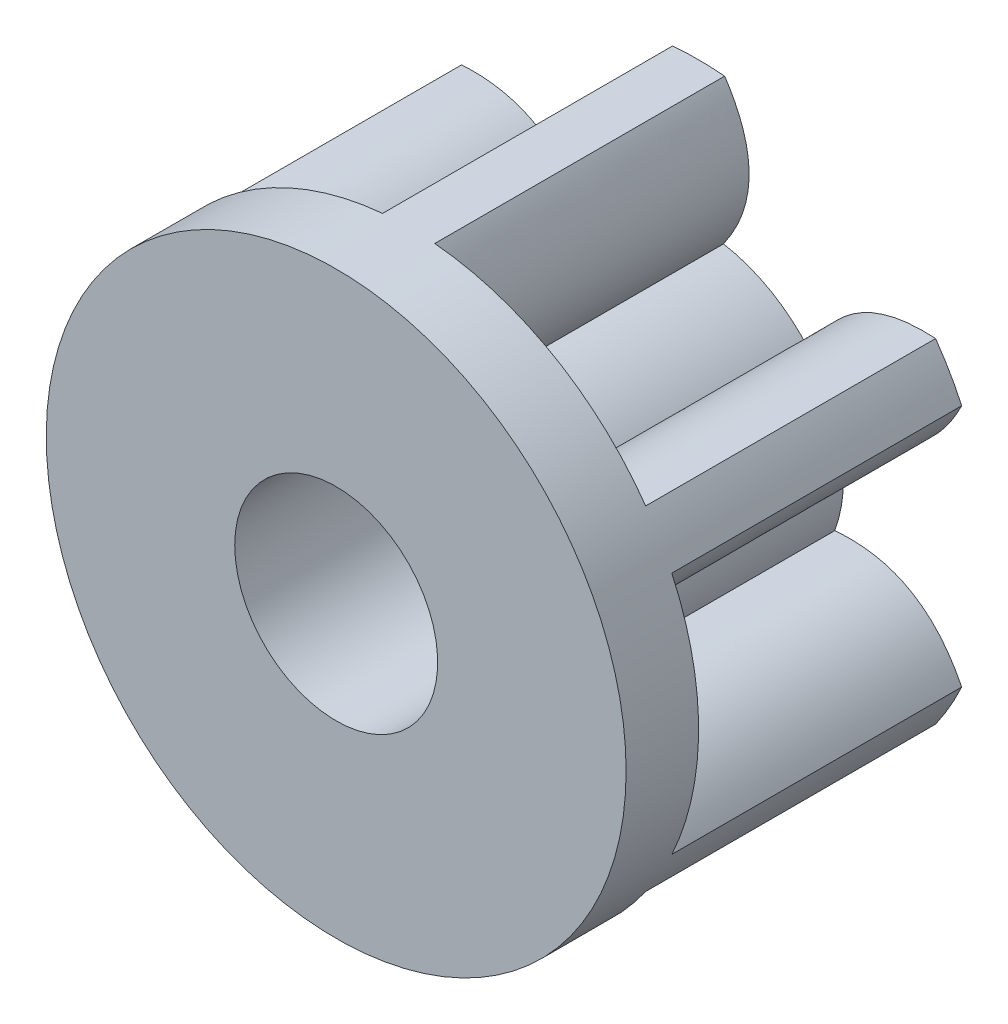
SolidWorks part; units mm, degrees
ref_plane "Front" through (0, 0, 0) normal (0, 0, 1) x (1, 0, 0)
ref_plane "Top" through (0, 0, 0) normal (0, 1, 0) x (1, 0, 0)
ref_plane "Right" through (0, 0, 0) normal (1, 0, 0) x (0, 0, -1)
sketch "草图1" plane through (0, 0, 0) normal (0, 0, 1) x (1, 0, 0)
  line L0 (0, 0) -> (0, 2.8571) construction
  line L1 (0, 0) -> (-0.4625, 2.6229) construction
  line L2 (0, 0) -> (0.5268, 2.9874) construction
  line L3 (0, 0) -> (1.1577, 3.1809) construction
  line L4 (0, 0) -> (-1.0433, 2.8663) construction
  arc A0 (-0.1714, 0.9852) -> (-0.7675, 0.641) centre (0, 0) ccw
  arc A1 (0.1798, 1.9919) -> (-0.18, 1.9919) centre (0, 0) ccw
  arc A2 (1.8149, 0.8402) -> (1.635, 1.1518) centre (0, 0) ccw
  arc A3 (1.6351, -1.1517) -> (1.815, -0.8401) centre (0, 0) ccw
  arc A4 (-0.1798, -1.9919) -> (0.18, -1.9919) centre (0, 0) ccw
  arc A5 (-1.8149, -0.8402) -> (-1.635, -1.1518) centre (0, 0) ccw
  arc A6 (-1.6351, 1.1517) -> (-1.815, 0.8401) centre (0, 0) ccw
  arc A7 (-0.9389, 0.3442) -> (-0.9389, -0.3442) centre (0, 0) ccw
  arc A8 (0.7675, 0.641) -> (0.1714, 0.9852) centre (0, 0) ccw
  arc A9 (-0.7675, -0.641) -> (-0.1714, -0.9852) centre (0, 0) ccw
  arc A10 (0.9389, -0.3442) -> (0.9389, 0.3442) centre (0, 0) ccw
  arc A11 (0.1714, -0.9852) -> (0.7675, -0.641) centre (0, 0) ccw
  spline S0 degree 2 poles (-0.18, 1.9919) (-0.5208, 1.4797) (-0.1714, 0.9852) knots 0 0 0 1 1 1
  spline S1 degree 2 poles (0.1798, 1.9919) (0.5209, 1.4798) (0.1714, 0.9852) knots 0 0 0 1 1 1
  spline S2 degree 2 poles (1.8149, 0.8402) (1.542, 0.2888) (0.9389, 0.3442) knots 0 0 0 1 1 1
  spline S3 degree 2 poles (1.635, 1.1518) (1.0211, 1.1909) (0.7675, 0.641) knots 0 0 0 1 1 1
  spline S4 degree 2 poles (1.6351, -1.1517) (1.0211, -1.191) (0.7675, -0.641) knots 0 0 0 1 1 1
  spline S5 degree 2 poles (1.815, -0.8401) (1.5419, -0.2888) (0.9389, -0.3442) knots 0 0 0 1 1 1
  spline S6 degree 2 poles (-0.1798, -1.9919) (-0.5209, -1.4798) (-0.1714, -0.9852) knots 0 0 0 1 1 1
  spline S7 degree 2 poles (0.18, -1.9919) (0.5208, -1.4797) (0.1714, -0.9852) knots 0 0 0 1 1 1
  spline S8 degree 2 poles (-1.8149, -0.8402) (-1.542, -0.2888) (-0.9389, -0.3442) knots 0 0 0 1 1 1
  spline S9 degree 2 poles (-1.635, -1.1518) (-1.0211, -1.1909) (-0.7675, -0.641) knots 0 0 0 1 1 1
  spline S10 degree 2 poles (-1.6351, 1.1517) (-1.0211, 1.191) (-0.7675, 0.641) knots 0 0 0 1 1 1
  spline S11 degree 2 poles (-1.815, 0.8401) (-1.5419, 0.2888) (-0.9389, 0.3442) knots 0 0 0 1 1 1
  point P5 (0, 2)
  point P11 (-0.18, 1.9919)
  point P12 (0.1798, 1.9919)
  point P13 (0, 1.5)
  point P14 (-0.3476, 1.4592)
  point P15 (0.3476, 1.4592)
  point P16 (0, 1)
  point P17 (-0.1714, 0.9852)
  point P18 (0.1714, 0.9852)
  point P54 (0, 0)
  dimension "D1" = 2
  dimension "D2" = 4
  dimension "D3" = 6
  dimension "D4" = 0.18
  dimension "D5" = 0.18
  dimension "D6" = 0.35
  dimension "D7" = 0.35
extrude "凸台-拉伸1" add sketch "草图1" along normal blind 2
sketch "草图2" plane through (0, 0, 2) normal (0, 0, 1) x (1, 0, 0)
  circle A0 centre (0, 0) radius 2
  dimension "D1" = 4
extrude "凸台-拉伸2" add sketch "草图2" along normal blind 0.5
sketch "草图3" plane through (0, 0, 0) normal (0, 0, -1) x (-1, 0, 0)
  circle A0 centre (0, 0) radius 0.7
extrude "切除-拉伸1" cut sketch "草图3" against normal through all
